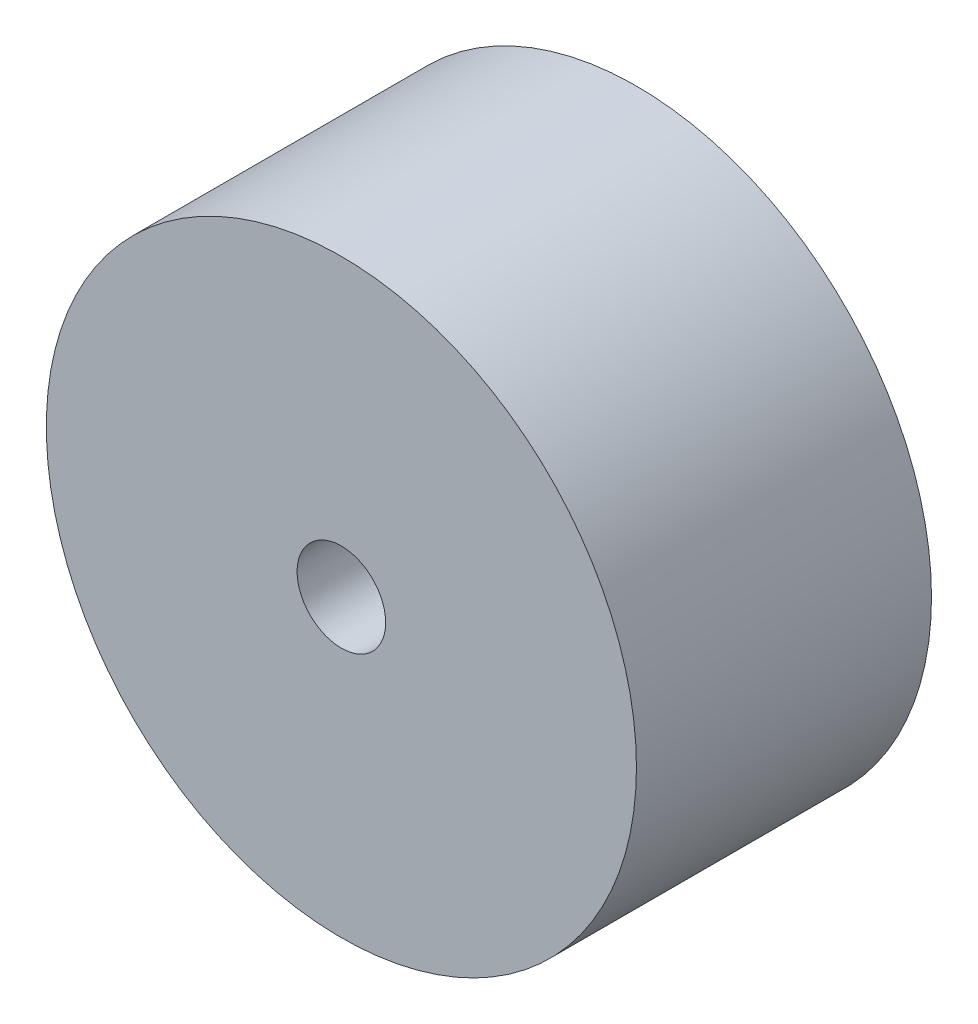
SolidWorks part; units mm, degrees
ref_plane "Plan de face" through (0, 0, 0) normal (0, 0, 1) x (1, 0, 0)
ref_plane "Plan de dessus" through (0, 0, 0) normal (0, 1, 0) x (1, 0, 0)
ref_plane "Plan de droite" through (0, 0, 0) normal (1, 0, 0) x (0, 0, -1)
sketch "Esquisse1" plane through (0, 0, 0) normal (0, 0, 1) x (1, 0, 0)
  circle A0 centre (0, 0) radius 10
  circle A1 centre (0, 0) radius 1.5
  dimension "D1" = 3
  dimension "D2" = 20
extrude "Boss.-Extru.1" add sketch "Esquisse1" along normal blind 10
